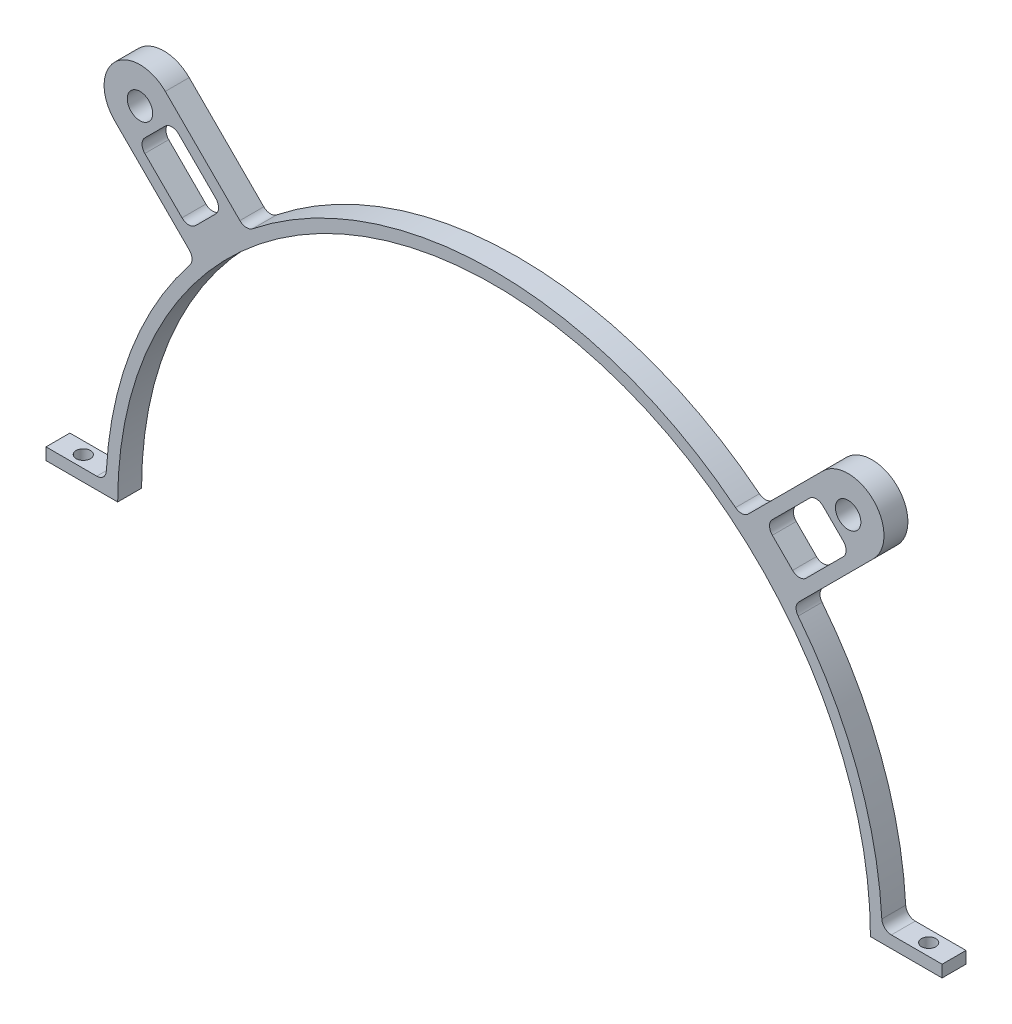
SolidWorks part; units mm, degrees
material "6061-T6 (SS)"
ref_plane "Front Plane" through (0, 0, 0) normal (0, 0, 1) x (1, 0, 0)
ref_plane "Top Plane" through (0, 0, 0) normal (0, 1, 0) x (1, 0, 0)
ref_plane "Right Plane" through (0, 0, 0) normal (1, 0, 0) x (0, 0, -1)
sketch "Sketch1" plane through (0, 0, 0) normal (0, 0, 1) x (1, 0, 0)
  line L0 (-100.0379, 0) -> (-119.0879, 0)
  line L1 (100.0379, 0) -> (119.0879, 0)
  line L2 (103.1641, 3.175) -> (119.0879, 3.175)
  line L3 (-103.1641, 3.175) -> (-119.0879, 3.175)
  line L4 (-119.0879, 3.175) -> (-119.0879, 0)
  line L5 (119.0879, 3.175) -> (119.0879, 0)
  arc A0 (100.0379, 0) -> (-100.0379, 0) centre (0, 0) ccw
  arc A1 (103.1641, 3.175) -> (-103.1641, 3.175) centre (0, 0) ccw
  dimension "D1" = 100.0379
  dimension "D2" = 19.05
  dimension "D3" = 19.05
  dimension "D4" = 3.175
extrude "Boss-Extrude1" add sketch "Sketch1" along normal blind 6.35
fillet "Fillet1" radius 2.54 2 edges at (103.1641, 3.175, 3.175) (-103.1641, 3.175, 3.175)
sketch "Sketch2" plane through (0, 0, 6.35) normal (0, 0, 1) x (1, 0, 0)
  line L0 (0, 0) -> (-94.1131, 94.1131) construction
  line L1 (-100.8483, 87.3779) -> (-87.3779, 100.8483) construction
  line L2 (-100.8483, 87.3779) -> (-79.4063, 65.9359)
  line L3 (-87.3779, 100.8483) -> (-65.9359, 79.4063)
  line L4 (-79.4063, 65.9359) -> (-70.7375, 70.7375)
  line L5 (-70.7375, 70.7375) -> (-65.9359, 79.4063)
  line L6 (-90.1273, 76.6569) -> (-76.6569, 90.1273) construction
  line L7 (-94.6174, 85.6372) -> (-85.6372, 94.6174)
  line L8 (-85.6372, 94.6174) -> (-72.1668, 81.147)
  line L9 (-72.1668, 81.147) -> (-81.147, 72.1668)
  line L10 (-81.147, 72.1668) -> (-94.6174, 85.6372)
  arc A0 (-87.3779, 100.8483) -> (-100.8483, 87.3779) centre (-94.1131, 94.1131) ccw
  arc A1 (103.0621, 5.5777) -> (-103.0621, 5.5777) centre (0, 0) ccw construction
  arc A2 (100.0379, 0) -> (-100.0379, 0) centre (0, 0) ccw construction
  dimension "D2" = 9.525
  dimension "D1" = 133.096
  dimension "D3" = 94.1131
  dimension "D4" = 12.7
  dimension "D5" = 19.05
  dimension "D6" = 9.525
  dimension "D7" = 6.35
extrude "Boss-Extrude2" add sketch "Sketch2" against normal blind 6.35
fillet "Fillet2" radius 2.54 6 edges at (-65.9359, 79.4063, 3.175) (-79.4063, 65.9359, 3.175) (-81.147, 72.1668, 3.175) (-72.1668, 81.147, 3.175) (-85.6372, 94.6174, 3.175) (-94.6174, 85.6372, 3.175)
hole_wizard "1/4 Clearance Hole1" positions "Sketch4" profile "Sketch3" hole size "1/4" standard "Ansi Inch"
sketch "Sketch4" plane through (0, 0, 6.35) normal (0, 0, 1) x (1, 0, 0)
  point P0 (-94.1131, 94.1131)
sketch "Sketch3" plane through (-94.1131, 94.1131, 6.35) normal (1, 0, 0) x (0, -1, 0)
  line L0 (0, 0) -> (0, 27.4298)
  line L1 (0, 27.4298) -> (3.3782, 25.4)
  line L2 (3.3782, 25.4) -> (3.3782, 0)
  line L5 (3.3782, 0) -> (0, 0)
  line L10 (0, 27.4298) -> (-3.3782, 25.4) construction
  line L11 (0, -6.35) -> (0, 107.95) construction
  dimension "Hole Dia." = 6.7564
  dimension "Hole Depth" = 25.4
  dimension "Drill Angle" = 118
hole_wizard "#6 Clearance Hole1" positions "Sketch6" profile "Sketch5" hole size "#6" standard "Ansi Inch"
sketch "Sketch6" plane through (0, 3.175, 0) normal (0, 1, 0) x (-1, 0, 0)
  line L0 (119.0879, 3.175) -> (105.5984, 3.175) construction
  line L1 (119.0879, 6.35) -> (119.0879, 0) construction
  line L2 (105.5984, 6.35) -> (105.5984, 0) construction
  point P0 (112.3431, 3.175)
sketch "Sketch5" plane through (-112.3431, 3.175, 3.175) normal (1, 0, 0) x (0, 0, 1)
  line L0 (0, 0) -> (0, 26.5408)
  line L1 (0, 26.5408) -> (1.8986, 25.4)
  line L2 (1.8986, 25.4) -> (1.8986, 0)
  line L5 (1.8986, 0) -> (0, 0)
  line L10 (0, 26.5408) -> (-1.8987, 25.4) construction
  line L11 (0, -6.35) -> (0, 107.95) construction
  dimension "Hole Dia." = 3.7973
  dimension "Hole Depth" = 25.4
  dimension "Drill Angle" = 118
mirror "Mirror1" about plane through (0, 0, 0) normal (1, 0, 0) of "#6 Clearance Hole1", "1/4 Clearance Hole1", "Fillet2", "Boss-Extrude2"
